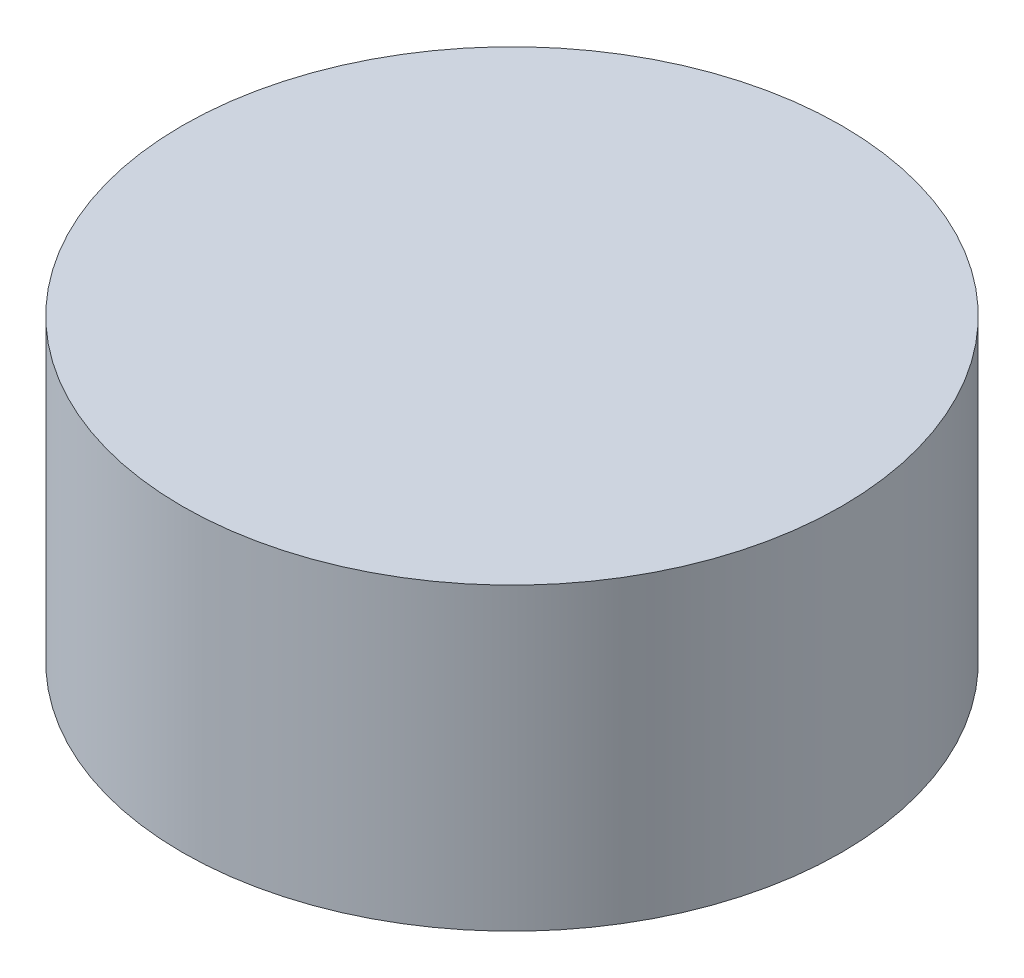
SolidWorks part; units mm, degrees
ref_plane "Front Plane" through (0, 0, 0) normal (0, 0, 1) x (1, 0, 0)
ref_plane "Top Plane" through (0, 0, 0) normal (0, 1, 0) x (1, 0, 0)
ref_plane "Right Plane" through (0, 0, 0) normal (1, 0, 0) x (0, 0, -1)
sketch "Sketch1" plane through (0, 0, 0) normal (0, 1, 0) x (1, 0, 0)
  circle A0 centre (0, 0) radius 5.588
  dimension "D1" = 11.176
extrude "Boss-Extrude1" add sketch "Sketch1" along normal blind 5.08
